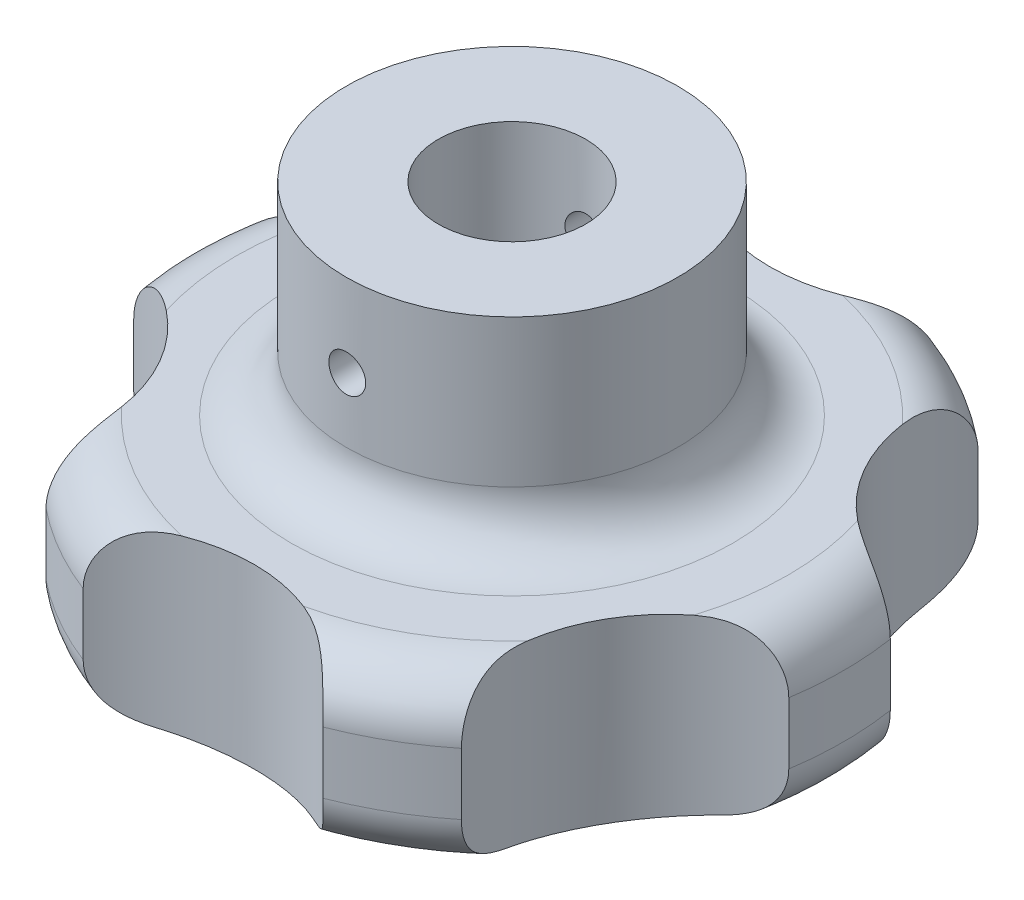
SolidWorks part; units mm, degrees
ref_plane "Front Plane" through (0, 0, 0) normal (0, 0, 1) x (1, 0, 0)
ref_plane "Top Plane" through (0, 0, 0) normal (0, 1, 0) x (1, 0, 0)
ref_plane "Right Plane" through (0, 0, 0) normal (1, 0, 0) x (0, 0, -1)
sketch "Sketch1" plane through (0, 0, 0) normal (0, 0, 1) x (1, 0, 0)
  line L0 (0, 0) -> (0, 34.925) construction
  line L1 (0, 14.2875) -> (6.35, 16.5987)
  line L2 (6.35, 16.5987) -> (6.35, 34.925)
  line L3 (6.35, 34.925) -> (14.2875, 34.925)
  line L4 (14.2875, 34.925) -> (14.2875, 22.225)
  line L5 (19.05, 17.4625) -> (23.8125, 17.4625)
  line L6 (28.575, 12.7) -> (28.575, 7.3821)
  line L7 (0, 0) -> (28.575, 0) construction
  line L8 (0, 0) -> (0, 14.2875)
  arc A0 (0, 0) -> (24.8478, 2.7335) centre (0, 114.3) ccw
  arc A1 (28.575, 7.3821) -> (24.8478, 2.7335) centre (23.8125, 7.3821) cw
  arc A2 (23.8125, 17.4625) -> (28.575, 12.7) centre (23.8125, 12.7) cw
  arc A3 (14.2875, 22.225) -> (19.05, 17.4625) centre (19.05, 22.225) ccw
  point P18 (28.575, 3.6295)
  dimension "D4" = 114.3
  dimension "D9" = 4.7625
  dimension "D1" = 34.925
  dimension "D2" = 28.575
  dimension "D3" = 17.4625
  dimension "D5" = 14.2875
  dimension "D6" = 6.35
  dimension "D7" = 20.6375
  dimension "D8" = 110
revolve "Revolve1" add sketch "Sketch1" angle 360 about L0
sketch "Sketch2" plane through (0, 0, 0) normal (0, 1, 0) x (1, 0, 0)
  line L0 (0, -36.5125) -> (0, 28.575) construction
  line L1 (0, 0) -> (-10.3302, -26.6424) construction
  line L2 (0, 0) -> (-28.2381, -4.375) construction
  arc A2 (-10.3302, -26.6424) -> (10.3302, -26.6424) centre (0, -36.5125) cw
  circle A3 centre (0, 0) radius 28.575 construction
  arc A4 (-28.2381, -4.375) -> (-17.9079, -22.2674) centre (-31.6208, -18.2562) cw
  arc A5 (-17.9079, 22.2674) -> (-28.2381, 4.375) centre (-31.6208, 18.2563) cw
  arc A6 (10.3302, 26.6424) -> (-10.3302, 26.6424) centre (0, 36.5125) cw
  arc A7 (28.2381, 4.375) -> (17.9079, 22.2674) centre (31.6208, 18.2562) cw
  arc A8 (17.9079, -22.2674) -> (28.2381, -4.375) centre (31.6208, -18.2563) cw
  circle A9 centre (0, 0) radius 28.575
  dimension "D1" = 14.2875
  dimension "D2" = 22.225
  dimension "D4" = 60
  dimension "D3" = 6
extrude "Cut-Extrude1" cut sketch "Sketch2" along normal up to next contours A4 A9 | A2 A9 | A8 A9 | A7 A9 | A6 A9 | A5 A9
sketch "Sketch3" plane through (0, 0, 0) normal (0, 0, 1) x (1, 0, 0)
  line L0 (6.35, 34.925) -> (-6.35, 34.925) construction
  circle A0 centre (0, 27.7812) radius 1.5875
  dimension "D1" = 3.175
  dimension "D2" = 7.1437
extrude "Cut-Extrude2" cut sketch "Sketch3" against normal through all both and the other way through all
